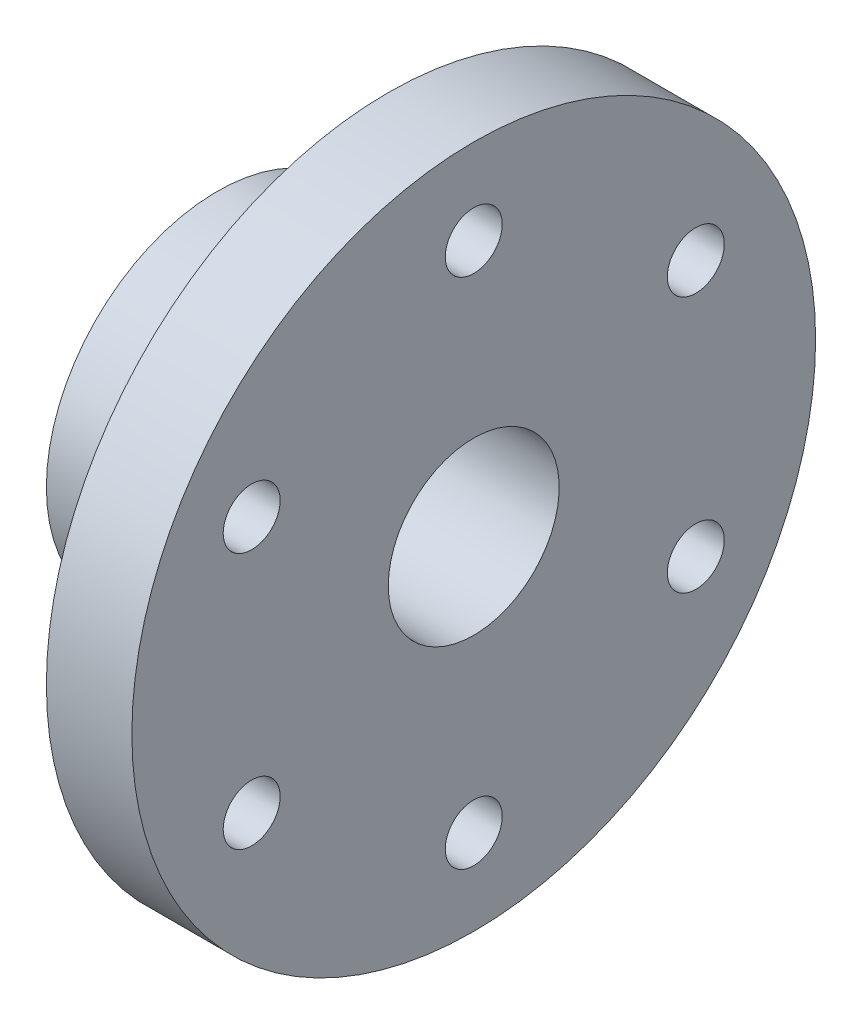
SolidWorks part; units mm, degrees
ref_plane "Front Plane" through (0, 0, 0) normal (0, 0, 1) x (1, 0, 0)
ref_plane "Top Plane" through (0, 0, 0) normal (0, 1, 0) x (1, 0, 0)
ref_plane "Right Plane" through (0, 0, 0) normal (1, 0, 0) x (0, 0, -1)
sketch "Sketch1" plane through (0, 0, 0) normal (0, 0, 1) x (1, 0, 0)
  line L0 (-11.6129, 0) -> (15.7189, 0) construction
  line L1 (-25.7005, 12) -> (-25.7005, 24)
  line L2 (-25.7005, 24) -> (-1.7005, 24)
  line L3 (-1.7005, 24) -> (-1.7005, 48)
  line L4 (-1.7005, 48) -> (10.2995, 48)
  line L5 (10.2995, 48) -> (10.2995, 12)
  line L6 (10.2995, 12) -> (-25.7005, 12)
  dimension "D1" = 48
  dimension "D2" = 12
  dimension "D3" = 24
  dimension "D4" = 24
  dimension "D5" = 12
revolve "Revolve1" add sketch "Sketch1" angle 360 about L0
sketch "Sketch2" plane through (-1.7005, 0, 0) normal (-1, 0, 0) x (0, 0, 1)
  line L0 (0, -36) -> (0, 36) construction
  line L1 (-31.1769, 18) -> (31.1769, -18) construction
  line L2 (31.1769, 18) -> (-31.1769, -18) construction
  circle A0 centre (0, 0) radius 36 construction
  circle A9 centre (0, 36) radius 4
  circle A10 centre (31.1769, 18) radius 4
  circle A11 centre (31.1769, -18) radius 4
  circle A12 centre (0, -36) radius 4
  circle A13 centre (-31.1769, -18) radius 4
  circle A14 centre (-31.1769, 18) radius 4
  point P22 (0, 0)
  dimension "D1" = 72
  dimension "D4" = 8
  dimension "D5" = 6
extrude "Cut-Extrude1" cut sketch "Sketch2" against normal up to surface (12 mm away) up to face at (10.2995, 0, 48)
ref_plane "Plane1" through (0, 0, 24) normal (0, 0, 1) x (1, 0, 0)
sketch "Sketch3" plane through (0, 0, 24) normal (0, 0, 1) x (1, 0, 0)
  line L0 (-25.7005, 0) -> (-1.7005, 0) construction
  line L1 (-25.7005, 24) -> (-25.7005, -24) construction
  line L2 (-1.7005, 48) -> (-1.7005, -48) construction
  circle A0 centre (-13.7005, 0) radius 4
  dimension "D1" = 8
extrude "Cut-Extrude2" cut sketch "Sketch3" against normal up to surface (12 mm away) up to face at (10.2995, 0, 12)
sketch "Sketch4" plane through (-25.7005, 0, 0) normal (-1, 0, 0) x (0, 0, 1)
  circle A0 centre (0, 0) radius 8.5
